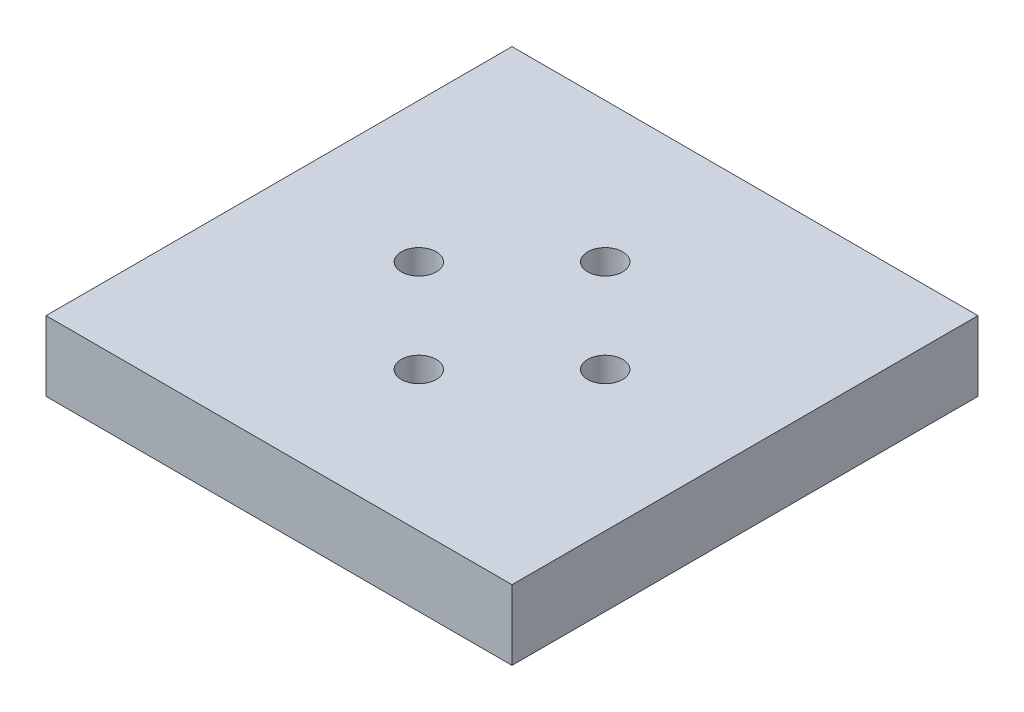
SolidWorks part; units mm, degrees
ref_plane "Front Plane" through (0, 0, 0) normal (0, 0, 1) x (1, 0, 0)
ref_plane "Top Plane" through (0, 0, 0) normal (0, 1, 0) x (1, 0, 0)
ref_plane "Right Plane" through (0, 0, 0) normal (1, 0, 0) x (0, 0, -1)
sketch "Sketch1" plane through (0, 0, 0) normal (0, 1, 0) x (1, 0, 0)
  line L1 (-20, -20) -> (20, -20)
  line L2 (-20, -20) -> (-20, 20)
  line L3 (-20, 20) -> (20, 20)
  line L4 (20, -20) -> (20, 20)
  line L5 (-20, -20) -> (20, 20) construction
  line L6 (-20, 20) -> (20, -20) construction
  circle A0 centre (0, 0) radius 8 construction
  circle A1 centre (0, 8) radius 1.5
  circle A2 centre (8, 0) radius 1.5
  circle A3 centre (0, -8) radius 1.5
  circle A4 centre (-8, 0) radius 1.5
  point P14 (0, 0)
  dimension "D1" = 16
  dimension "D2" = 3
  dimension "D4" = 40
  dimension "D5" = 40
  dimension "D3" = 4
extrude "Boss-Extrude1" add sketch "Sketch1" along normal blind 3
sketch "Sketch2" plane through (0, 0, 0) normal (0, -1, 0) x (1, 0, 0)
  line L0 (-16, 16) -> (-16, -16)
  line L1 (-20, 20) -> (20, 20)
  line L2 (-20, 20) -> (-20, -20)
  line L3 (-20, -20) -> (20, -20)
  line L4 (20, 20) -> (20, -20)
  line L5 (-16, -16) -> (16, -16)
  line L6 (16, 16) -> (16, -16)
  line L7 (-16, 16) -> (16, 16)
  dimension "D1" = 4
extrude "Boss-Extrude2" add sketch "Sketch2" along normal blind 3
